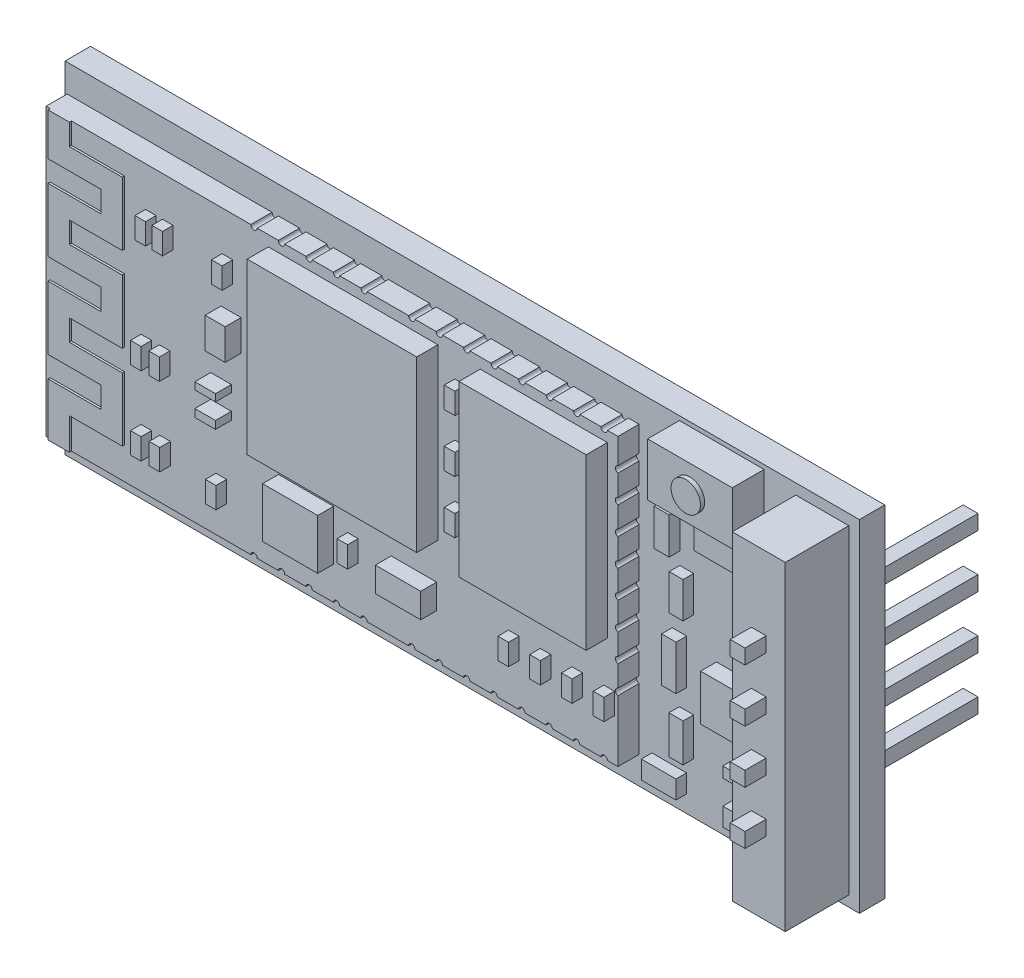
SolidWorks part; units mm, degrees
material "E-Glass Fiber"
ref_plane "Top Plane" through (0, 0, 0) normal (0, 0, 1) x (1, 0, 0)
ref_plane "Front Plane" through (0, 0, 0) normal (0, 1, 0) x (1, 0, 0)
ref_plane "Right Plane" through (0, 0, 0) normal (1, 0, 0) x (0, 0, -1)
sketch "Sketch1" plane through (0, 0, 0) normal (0, 0, 1) x (1, 0, 0)
  line L1 (0, 0) -> (37.5, 0)
  line L2 (0, 0) -> (0, 16.1)
  line L3 (0, 16.1) -> (37.5, 16.1)
  line L4 (37.5, 0) -> (37.5, 16.1)
  dimension "D1" = 37.5
  dimension "D2" = 16.1
extrude "Boss-Extrude1" add sketch "Sketch1" along normal blind 1.2
sketch "Sketch2" plane through (0, 0, 1.2) normal (0, 0, 1) x (1, 0, 0)
  line L0 (37.5, 0) -> (37.5, 16.1) construction
  line L1 (34.5, 0.5) -> (37, 0.5)
  line L2 (34.5, 0.5) -> (34.5, 15.6)
  line L3 (34.5, 15.6) -> (37, 15.6)
  line L4 (37, 0.5) -> (37, 15.6)
  line L5 (0, 0) -> (37.5, 0) construction
  line L6 (37.5, 16.1) -> (0, 16.1) construction
  dimension "D1" = 0.5
  dimension "D2" = 0.5
  dimension "D3" = 0.5
  dimension "D4" = 2.5
extrude "Boss-Extrude2" add sketch "Sketch2" along normal blind 3
sketch "Sketch3" plane through (0, 0, 4.2) normal (0, 0, 1) x (1, 0, 0)
  line L0 (34.5, 3.05) -> (37, 3.05)
  line L1 (34.5, 15.6) -> (34.5, 0.5) construction
  line L3 (34.5, 5.55) -> (37, 5.55)
  line L4 (37, 0.5) -> (37, 15.6) construction
  line L5 (34.5, 8.05) -> (37, 8.05)
  line L6 (34.5, 10.55) -> (37, 10.55)
  line L7 (34.5, 15.6) -> (34.5, 0.5) construction
  line L8 (34.5, 13.05) -> (37, 13.05)
  line L9 (37, 0.5) -> (37, 15.6) construction
  line L10 (34.5, 0.55) -> (37, 0.55)
  line L11 (34.5, 15.55) -> (37, 15.55)
  line L12 (37, 15.6) -> (34.5, 15.6) construction
  line L13 (34.5, 0.5) -> (37, 0.5) construction
  line L14 (35.4, 4.65) -> (36.1, 4.65)
  line L15 (35.4, 2.15) -> (36.1, 2.15) construction
  line L16 (35.4, 2.15) -> (35.4, 1.45) construction
  line L17 (35.4, 1.45) -> (36.1, 1.45) construction
  line L18 (36.1, 2.15) -> (36.1, 1.45) construction
  line L19 (35.4, 4.65) -> (35.4, 3.95)
  line L20 (35.4, 3.95) -> (36.1, 3.95)
  line L21 (36.1, 4.65) -> (36.1, 3.95)
  line L22 (35.4, 7.15) -> (36.1, 7.15)
  line L23 (35.4, 7.15) -> (35.4, 6.45)
  line L24 (35.4, 6.45) -> (36.1, 6.45)
  line L25 (36.1, 7.15) -> (36.1, 6.45)
  line L26 (35.4, 12.15) -> (36.1, 12.15)
  line L27 (35.4, 12.15) -> (35.4, 11.45)
  line L28 (35.4, 11.45) -> (36.1, 11.45)
  line L29 (36.1, 12.15) -> (36.1, 11.45)
  line L30 (35.4, 9.65) -> (36.1, 9.65)
  line L31 (35.4, 9.65) -> (35.4, 8.95)
  line L32 (35.4, 8.95) -> (36.1, 8.95)
  line L33 (36.1, 9.65) -> (36.1, 8.95)
  line L34 (35.4, 14.65) -> (36.1, 14.65) construction
  line L35 (35.4, 14.65) -> (35.4, 13.95) construction
  line L36 (35.4, 13.95) -> (36.1, 13.95) construction
  line L37 (36.1, 14.65) -> (36.1, 13.95) construction
  dimension "D1" = 0.05
  dimension "D2" = 0.05
  dimension "D3" = 2.5
  dimension "D4" = 2.5
  dimension "D5" = 2.5
  dimension "D6" = 2.5
  dimension "D7" = 2.5
  dimension "D8" = 0.7
  dimension "D9" = 0.7
  dimension "D10" = 0.9
  dimension "D11" = 0.9
  dimension "D12" = 0.7
  dimension "D13" = 0.7
  dimension "D14" = 0.9
  dimension "D15" = 0.9
  dimension "D16" = 0.9
  dimension "D17" = 0.9
  dimension "D18" = 0.7
  dimension "D19" = 0.7
  dimension "D20" = 0.9
  dimension "D21" = 0.9
  dimension "D22" = 0.7
  dimension "D23" = 0.7
  dimension "D24" = 0.9
  dimension "D25" = 0.9
  dimension "D26" = 0.7
  dimension "D27" = 0.7
  dimension "D28" = 0.9
  dimension "D29" = 0.7
  dimension "D30" = 0.9
  dimension "D31" = 0.7
extrude "Boss-Extrude3" add sketch "Sketch3" along normal blind 1 and the other way blind 10 separate body contours L18 L15 L16 L17 | L21 L14 L19 L20 | L33 L30 L31 L32 | L29 L26 L27 L28 | L37 L34 L35 L36 | L25 L24 L23 L22
sketch "Sketch10" plane through (0, 0, 1.2) normal (0, 0, 1) x (1, 0, 0)
  line L1 (0.1, 14.8) -> (27.1, 14.8)
  line L2 (0.1, 14.8) -> (0.1, 1.3)
  line L3 (0.1, 1.3) -> (27.1, 1.3)
  line L4 (27.1, 14.8) -> (27.1, 1.3)
  line L5 (37.5, 16.1) -> (0, 16.1) construction
  line L7 (0, 16.1) -> (0, 0) construction
  point P6 (0, 8.05)
  dimension "D1" = 13.5
  dimension "D2" = 27
  dimension "D3" = 1.3
  dimension "D4" = 0.1
extrude "Boss-Extrude10" add sketch "Sketch10" along normal blind 1
sketch "Sketch11" plane through (0, 0, 2.2) normal (0, 0, 1) x (1, 0, 0)
  line L0 (0.3, 1.3) -> (0.3, 14.8) construction
  line L1 (0.1, 1.3) -> (27.1, 1.3) construction
  line L2 (27.1, 14.8) -> (0.1, 14.8) construction
  line L3 (0.1, 14.8) -> (0.1, 1.3) construction
  line L4 (3.8, 14.8) -> (3.8, 1.3) construction
  line L5 (0.3, 1.3) -> (0.3, 3.8)
  line L6 (1.3, 2.8) -> (3.8, 2.8)
  line L7 (3.8, 2.8) -> (3.8, 5.8)
  line L8 (0.3, 3.8) -> (2.8, 3.8)
  line L9 (1.3, 1.3) -> (1.3, 2.8)
  line L10 (0.1, 1.3) -> (27.1, 1.3) construction
  line L11 (2.8, 3.8) -> (2.8, 4.8)
  line L12 (2.8, 4.8) -> (0.3, 4.8)
  line L13 (0.3, 4.8) -> (0.3, 7.8)
  line L14 (0.3, 7.8) -> (2.8, 7.8)
  line L15 (3.8, 5.8) -> (1.3, 5.8)
  line L16 (1.3, 5.8) -> (1.3, 6.8)
  line L17 (1.3, 6.8) -> (3.8, 6.8)
  line L18 (3.8, 6.8) -> (3.8, 9.8)
  line L19 (2.8, 7.8) -> (2.8, 8.8)
  line L20 (2.8, 8.8) -> (0.3, 8.8)
  line L21 (0.3, 8.8) -> (0.3, 11.8)
  line L22 (3.8, 9.8) -> (1.3, 9.8)
  line L23 (1.3, 9.8) -> (1.3, 10.8)
  line L24 (1.3, 10.8) -> (3.8, 10.8)
  line L25 (3.8, 10.8) -> (3.8, 13.8)
  line L26 (0.3, 11.8) -> (2.8, 11.8)
  line L27 (2.8, 11.8) -> (2.8, 12.8)
  line L28 (2.8, 12.8) -> (0.3, 12.8)
  line L29 (0.3, 12.8) -> (0.3, 14.8)
  line L30 (3.8, 13.8) -> (1.3, 13.8)
  line L31 (1.3, 13.8) -> (1.3, 14.8)
  line L32 (1.3, 14.8) -> (0.3, 14.8)
  line L33 (1.3, 1.3) -> (0.3, 1.3)
  dimension "D1" = 0.2
  dimension "D2" = 3.5
  dimension "D3" = 2.5
  dimension "D4" = 1
  dimension "D5" = 1.5
  dimension "D6" = 3
  dimension "D7" = 1
  dimension "D8" = 1
  dimension "D9" = 1
  dimension "D10" = 1
  dimension "D11" = 1
  dimension "D12" = 2.5
  dimension "D13" = 3
  dimension "D14" = 2.5
  dimension "D15" = 3
  dimension "D16" = 1
  dimension "D17" = 1
  dimension "D18" = 1
  dimension "D19" = 2.5
  dimension "D20" = 2.5
  dimension "D21" = 1
  dimension "D22" = 3
  dimension "D23" = 1
extrude "Boss-Extrude11" add sketch "Sketch11" along normal blind 0.1
sketch "Sketch12" plane through (0, 0, 1.2) normal (0, 0, 1) x (1, 0, 0)
  line L0 (37.5, 16.1) -> (0, 16.1) construction
  line L1 (29, 15.9) -> (33, 15.9)
  line L2 (29, 15.9) -> (29, 13.4)
  line L3 (29, 13.4) -> (33, 13.4)
  line L4 (33, 15.9) -> (33, 13.4)
  line L5 (34.5, 15.6) -> (34.5, 0.5) construction
  dimension "D1" = 2.5
  dimension "D2" = 4
  dimension "D3" = 0.2
  dimension "D4" = 1.5
extrude "Boss-Extrude12" add sketch "Sketch12" along normal blind 1.5 separate body
sketch "Sketch13" plane through (0, 0, 2.7) normal (0, 0, 1) x (1, 0, 0)
  line L0 (29, 14.65) -> (33, 14.65) construction
  line L1 (29, 15.9) -> (29, 13.4) construction
  line L2 (33, 13.4) -> (33, 15.9) construction
  line L3 (31, 15.9) -> (31, 13.4) construction
  line L4 (33, 15.9) -> (29, 15.9) construction
  line L5 (29, 13.4) -> (33, 13.4) construction
  circle A0 centre (31, 14.65) radius 0.6936
extrude "Boss-Extrude13" add sketch "Sketch13" along normal blind 0.2
sketch "Sketch14" plane through (0, 0, 2.2) normal (0, 0, 1) x (1, 0, 0)
  line L0 (27.1, 14.8) -> (1.3, 14.8) construction
  line L1 (26.6004, 6.3) -> (20.6004, 6.3)
  line L2 (26.6004, 6.3) -> (26.6004, 14.3)
  line L3 (26.6004, 14.3) -> (20.6004, 14.3)
  line L4 (20.6004, 6.3) -> (20.6004, 14.3)
  line L5 (27.1, 1.3) -> (27.1, 14.8) construction
  line L7 (18.6004, 6.3) -> (10.6004, 6.3)
  line L8 (18.6004, 6.3) -> (18.6004, 14.3)
  line L9 (18.6004, 14.3) -> (10.6004, 14.3)
  line L10 (10.6004, 6.3) -> (10.6004, 14.3)
  dimension "D1" = 8
  dimension "D2" = 6
  dimension "D3" = 0.5
  dimension "D4" = 0.4996
  dimension "D5" = 2
  dimension "D6" = 8
  dimension "D7" = 8
  dimension "D8" = 0.5
extrude "Boss-Extrude14" add sketch "Sketch14" along normal blind 1
sketch "Sketch15" plane through (0, 0, 2.2) normal (0, 0, 1) x (1, 0, 0)
  line L0 (3.8, 10.8) -> (3.8, 13.8) construction
  line L1 (4.8, 11.93) -> (5.3, 11.93)
  line L2 (4.8, 11.93) -> (4.8, 12.93)
  line L3 (4.8, 12.93) -> (5.3, 12.93)
  line L4 (5.3, 11.93) -> (5.3, 12.93)
  line L5 (5.6, 11.93) -> (6.1, 11.93)
  line L6 (5.6, 11.93) -> (5.6, 12.93)
  line L7 (5.6, 12.93) -> (6.1, 12.93)
  line L8 (6.1, 11.93) -> (6.1, 12.93)
  line L9 (8.4157, 11.93) -> (8.9157, 11.93)
  line L10 (8.4157, 11.93) -> (8.4157, 12.93)
  line L11 (8.4157, 12.93) -> (8.9157, 12.93)
  line L12 (8.9157, 11.93) -> (8.9157, 12.93)
  dimension "D1" = 1
  dimension "D2" = 0.5
  dimension "D3" = 1
  dimension "D4" = 0.5
  dimension "D5" = 1
  dimension "D6" = 0.5
  dimension "D7" = 1
  dimension "D8" = 0.3
extrude "Boss-Extrude15" add sketch "Sketch15" along normal blind 0.5
sketch "Sketch16" plane through (0, 0, 2.2) normal (0, 0, 1) x (1, 0, 0)
  line L0 (4.589, 6.722) -> (5.089, 6.722)
  line L1 (4.589, 6.722) -> (4.589, 7.722)
  line L2 (4.589, 7.722) -> (5.089, 7.722)
  line L3 (5.089, 6.722) -> (5.089, 7.722)
  line L4 (5.4516, 6.722) -> (5.9516, 6.722)
  line L5 (5.4516, 6.722) -> (5.4516, 7.722)
  line L6 (5.4516, 7.722) -> (5.9516, 7.722)
  line L7 (5.9516, 6.722) -> (5.9516, 7.722)
  line L8 (4.5888, 3.0335) -> (5.0888, 3.0335)
  line L9 (4.5888, 3.0335) -> (4.5888, 4.0335)
  line L10 (4.5888, 4.0335) -> (5.0888, 4.0335)
  line L11 (5.0888, 3.0335) -> (5.0888, 4.0335)
  line L12 (5.4701, 3.0335) -> (5.9701, 3.0335)
  line L13 (5.4701, 3.0335) -> (5.4701, 4.0335)
  line L14 (5.4701, 4.0335) -> (5.9701, 4.0335)
  line L15 (5.9701, 3.0335) -> (5.9701, 4.0335)
  line L16 (8.1243, 2.8062) -> (8.6243, 2.8062)
  line L17 (8.1243, 2.8062) -> (8.1243, 3.8062)
  line L18 (8.1243, 3.8062) -> (8.6243, 3.8062)
  line L19 (8.6243, 2.8062) -> (8.6243, 3.8062)
  line L20 (19.4004, 12.3) -> (19.9004, 12.3)
  line L21 (19.4004, 12.3) -> (19.4004, 13.3)
  line L22 (19.4004, 13.3) -> (19.9004, 13.3)
  line L23 (19.9004, 12.3) -> (19.9004, 13.3)
  line L24 (19.4004, 9.8) -> (19.9004, 9.8)
  line L25 (19.4004, 9.8) -> (19.4004, 10.8)
  line L26 (19.4004, 10.8) -> (19.9004, 10.8)
  line L27 (19.9004, 9.8) -> (19.9004, 10.8)
  line L28 (19.9004, 7.3) -> (19.4004, 7.3)
  line L29 (19.9004, 7.3) -> (19.9004, 8.3)
  line L30 (19.9004, 8.3) -> (19.4004, 8.3)
  line L31 (19.4004, 7.3) -> (19.4004, 8.3)
  line L32 (26.4351, 3.3) -> (26.9351, 3.3)
  line L33 (26.4351, 3.3) -> (26.4351, 4.3)
  line L34 (26.4351, 4.3) -> (26.9351, 4.3)
  line L35 (26.9351, 3.3) -> (26.9351, 4.3)
  line L36 (24.9351, 3.3) -> (25.4351, 3.3)
  line L37 (24.9351, 3.3) -> (24.9351, 4.3)
  line L38 (24.9351, 4.3) -> (25.4351, 4.3)
  line L39 (25.4351, 3.3) -> (25.4351, 4.3)
  line L40 (23.4351, 3.3) -> (23.9351, 3.3)
  line L41 (23.4351, 3.3) -> (23.4351, 4.3)
  line L42 (23.4351, 4.3) -> (23.9351, 4.3)
  line L43 (23.9351, 3.3) -> (23.9351, 4.3)
  line L44 (21.9351, 3.3) -> (22.4351, 3.3)
  line L45 (21.9351, 3.3) -> (21.9351, 4.3)
  line L46 (21.9351, 4.3) -> (22.4351, 4.3)
  line L47 (22.4351, 3.3) -> (22.4351, 4.3)
  line L48 (14.3404, 3.4908) -> (14.8404, 3.4908)
  line L49 (14.3404, 3.4908) -> (14.3404, 4.4908)
  line L50 (14.3404, 4.4908) -> (14.8404, 4.4908)
  line L51 (14.8404, 3.4908) -> (14.8404, 4.4908)
  line L52 (27.1, 14.8) -> (1.3, 14.8) construction
  line L54 (20.6004, 14.3) -> (20.6004, 6.3) construction
  line L55 (20.6004, 6.3) -> (26.6004, 6.3) construction
  dimension "D1" = 1
  dimension "D2" = 1
  dimension "D3" = 1
  dimension "D4" = 1
  dimension "D5" = 1
  dimension "D6" = 1
  dimension "D7" = 1
  dimension "D8" = 1
  dimension "D9" = 1
  dimension "D10" = 1
  dimension "D11" = 1
  dimension "D12" = 1
  dimension "D13" = 1
  dimension "D14" = 0.5
  dimension "D15" = 0.5
  dimension "D16" = 0.5
  dimension "D17" = 1.5
  dimension "D18" = 1.5
  dimension "D19" = 1.5
  dimension "D20" = 0.7
  dimension "D21" = 2
  dimension "D22" = 1
  dimension "D23" = 1
  dimension "D24" = 1
  dimension "D25" = 0.5
  dimension "D26" = 0.5
  dimension "D27" = 0.5
  dimension "D28" = 0.5
extrude "Boss-Extrude16" add sketch "Sketch16" along normal blind 0.5
sketch "Sketch17" plane through (0, 0, 2.2) normal (0, 0, 1) x (1, 0, 0)
  line L1 (11.0751, 2.8642) -> (13.6775, 2.8642)
  line L2 (11.0751, 2.8642) -> (11.0751, 5.2317)
  line L3 (11.0751, 5.2317) -> (13.6775, 5.2317)
  line L4 (13.6775, 2.8642) -> (13.6775, 5.2317)
  line L6 (16.3989, 3.3962) -> (18.5402, 3.3962)
  line L7 (16.3989, 3.3962) -> (16.3989, 4.5627)
  line L8 (16.3989, 4.5627) -> (18.5402, 4.5627)
  line L9 (18.5402, 3.3962) -> (18.5402, 4.5627)
  line L10 (7.8761, 6.3372) -> (8.8522, 6.3372)
  line L11 (7.8761, 6.3372) -> (7.8761, 6.7031)
  line L12 (7.8761, 6.7031) -> (8.8522, 6.7031)
  line L13 (8.8522, 6.3372) -> (8.8522, 6.7031)
  line L14 (7.8761, 7.4637) -> (8.8522, 7.4637)
  line L15 (7.8761, 7.4637) -> (7.8761, 7.7984)
  line L16 (7.8761, 7.7984) -> (8.8522, 7.7984)
  line L17 (8.8522, 7.4637) -> (8.8522, 7.7984)
  line L18 (8.3641, 9.3029) -> (9.3075, 9.3029)
  line L19 (8.3641, 9.3029) -> (8.3641, 10.7632)
  line L20 (8.3641, 10.7632) -> (9.3075, 10.7632)
  line L21 (9.3075, 9.3029) -> (9.3075, 10.7632)
extrude "Boss-Extrude17" add sketch "Sketch17" along normal blind 0.75
sketch "Sketch18" plane through (0, 0, 1.2) normal (0, 0, 1) x (1, 0, 0)
  line L1 (30.2001, 11.4276) -> (32.9069, 11.4276)
  line L2 (30.2001, 11.4276) -> (30.2001, 13.1705)
  line L3 (30.2001, 13.1705) -> (32.9069, 13.1705)
  line L4 (32.9069, 11.4276) -> (32.9069, 13.1705)
  line L5 (28.3044, 10.5724) -> (29.0208, 10.5724)
  line L6 (28.3044, 10.5724) -> (28.3044, 12.2991)
  line L7 (28.3044, 12.2991) -> (29.0208, 12.2991)
  line L8 (29.0208, 10.5724) -> (29.0208, 12.2991)
  line L9 (29.0208, 8.2903) -> (29.6736, 8.2903)
  line L10 (29.0208, 8.2903) -> (29.0208, 9.9841)
  line L11 (29.0208, 9.9841) -> (29.6736, 9.9841)
  line L12 (29.6736, 8.2903) -> (29.6736, 9.9841)
  line L13 (28.6626, 5.1548) -> (29.3472, 5.1548)
  line L14 (28.6626, 5.1548) -> (28.6626, 7.2612)
  line L15 (28.6626, 7.2612) -> (29.3472, 7.2612)
  line L16 (29.3472, 5.1548) -> (29.3472, 7.2612)
  line L17 (29.0049, 2.403) -> (29.6736, 2.403)
  line L18 (29.0049, 2.403) -> (29.0049, 4.2038)
  line L19 (29.0049, 4.2038) -> (29.6736, 4.2038)
  line L20 (29.6736, 2.403) -> (29.6736, 4.2038)
  line L21 (27.7053, 0.8007) -> (29.3393, 0.8007)
  line L22 (27.7053, 0.8007) -> (27.7053, 1.6631)
  line L23 (27.7053, 1.6631) -> (29.3393, 1.6631)
  line L24 (29.3393, 0.8007) -> (29.3393, 1.6631)
  line L25 (31.5535, 0.8007) -> (32.9069, 0.8007)
  line L26 (31.5535, 0.8007) -> (31.5535, 1.6631)
  line L27 (31.5535, 1.6631) -> (32.9069, 1.6631)
  line L28 (32.9069, 0.8007) -> (32.9069, 1.6631)
  line L29 (31.5535, 2.804) -> (32.9069, 2.804)
  line L30 (31.5535, 2.804) -> (31.5535, 3.3034)
  line L31 (31.5535, 3.3034) -> (32.9069, 3.3034)
  line L32 (32.9069, 2.804) -> (32.9069, 3.3034)
  line L33 (32.0202, 10.8077) -> (33.3885, 10.8077)
  line L34 (32.0202, 10.8077) -> (32.0202, 9.9841)
  line L35 (32.0202, 9.9841) -> (33.3885, 9.9841)
  line L36 (33.3885, 10.8077) -> (33.3885, 9.9841)
  line L37 (32.0202, 8.2903) -> (33.3885, 8.2903)
  line L38 (32.0202, 8.2903) -> (32.0202, 9.082)
  line L39 (32.0202, 9.082) -> (33.3885, 9.082)
  line L40 (33.3885, 8.2903) -> (33.3885, 9.082)
extrude "Boss-Extrude18" add sketch "Sketch18" along normal blind 0.5
sketch "Sketch19" plane through (0, 0, 1.2) normal (0, 0, 1) x (1, 0, 0)
  line L1 (30.7569, 4.7405) -> (33.8081, 4.7405)
  line L2 (30.7569, 4.7405) -> (30.7569, 6.9062)
  line L3 (30.7569, 6.9062) -> (33.8081, 6.9062)
  line L4 (33.8081, 4.7405) -> (33.8081, 6.9062)
extrude "Boss-Extrude19" add sketch "Sketch19" along normal blind 0.75
sketch "Sketch20" plane through (0, 0, 2.2) normal (0, 0, 1) x (1, 0, 0)
  line L0 (27.1, 14.8) -> (1.3, 14.8) construction
  line L1 (27.1, 1.3) -> (27.1, 14.8) construction
  line L2 (26.6, 14.8) -> (26.3, 14.8)
  line L3 (25.3, 14.8) -> (25.0045, 14.8)
  line L4 (24.5045, 14.4582) -> (24.5045, 15.2412) construction
  line L5 (23.7089, 14.8) -> (24.0045, 14.8)
  line L6 (22.4089, 14.8) -> (22.7089, 14.8)
  line L7 (21.9089, 14.5317) -> (21.9089, 15.1738) construction
  line L8 (21.4089, 14.8) -> (21.1089, 14.8)
  line L9 (20.1089, 14.8) -> (19.8134, 14.8)
  line L10 (18.5179, 14.8) -> (18.8134, 14.8)
  line L11 (17.2179, 14.8) -> (17.5179, 14.8)
  line L12 (16.2399, 14.5317) -> (16.2399, 15.1738) construction
  line L13 (10.5708, 14.5317) -> (10.5708, 15.1738) construction
  line L14 (15.2619, 14.8) -> (14.9619, 14.8)
  line L15 (13.9619, 14.8) -> (13.6663, 14.8)
  line L16 (12.3708, 14.8) -> (12.6663, 14.8)
  line L17 (11.0708, 14.8) -> (11.3708, 14.8)
  line L18 (10.0708, 14.8) -> (9.7708, 14.8)
  line L19 (27.1, 8.05) -> (0.1, 8.05) construction
  line L20 (0.1, 14.8) -> (0.1, 1.3) construction
  line L21 (10.5708, 1.5683) -> (10.5708, 0.9262) construction
  line L22 (16.2399, 1.5683) -> (16.2399, 0.9262) construction
  line L23 (21.9089, 1.5683) -> (21.9089, 0.9262) construction
  line L24 (24.5045, 1.6418) -> (24.5045, 0.8588) construction
  line L25 (10.0708, 1.3) -> (9.7708, 1.3)
  line L26 (11.0708, 1.3) -> (11.3708, 1.3)
  line L27 (12.3708, 1.3) -> (12.6663, 1.3)
  line L28 (13.9619, 1.3) -> (13.6663, 1.3)
  line L29 (15.2619, 1.3) -> (14.9619, 1.3)
  line L30 (17.2179, 1.3) -> (17.5179, 1.3)
  line L31 (18.5179, 1.3) -> (18.8134, 1.3)
  line L32 (20.1089, 1.3) -> (19.8134, 1.3)
  line L33 (21.4089, 1.3) -> (21.1089, 1.3)
  line L34 (22.4089, 1.3) -> (22.7089, 1.3)
  line L35 (23.7089, 1.3) -> (24.0045, 1.3)
  line L36 (25.3, 1.3) -> (25.0045, 1.3)
  line L37 (26.6, 1.3) -> (26.3, 1.3)
  arc A0 (26.6, 14.8) -> (26.3, 14.8) centre (26.45, 14.8) cw
  arc A1 (25.3, 14.8) -> (25.0045, 14.8) centre (25.1522, 14.8) cw
  arc A2 (23.7089, 14.8) -> (24.0045, 14.8) centre (23.8567, 14.8) ccw
  arc A3 (22.4089, 14.8) -> (22.7089, 14.8) centre (22.5589, 14.8) ccw
  arc A4 (21.4089, 14.8) -> (21.1089, 14.8) centre (21.2589, 14.8) cw
  arc A5 (20.1089, 14.8) -> (19.8134, 14.8) centre (19.9612, 14.8) cw
  arc A6 (18.5179, 14.8) -> (18.8134, 14.8) centre (18.6656, 14.8) ccw
  arc A7 (17.2179, 14.8) -> (17.5179, 14.8) centre (17.3679, 14.8) ccw
  arc A8 (15.2619, 14.8) -> (14.9619, 14.8) centre (15.1119, 14.8) cw
  arc A9 (13.9619, 14.8) -> (13.6663, 14.8) centre (13.8141, 14.8) cw
  arc A10 (12.3708, 14.8) -> (12.6663, 14.8) centre (12.5186, 14.8) ccw
  arc A11 (11.0708, 14.8) -> (11.3708, 14.8) centre (11.2208, 14.8) ccw
  arc A12 (10.0708, 14.8) -> (9.7708, 14.8) centre (9.9208, 14.8) cw
  arc A13 (10.0708, 1.3) -> (9.7708, 1.3) centre (9.9208, 1.3) ccw
  arc A14 (11.0708, 1.3) -> (11.3708, 1.3) centre (11.2208, 1.3) cw
  arc A15 (12.3708, 1.3) -> (12.6663, 1.3) centre (12.5186, 1.3) cw
  arc A16 (13.9619, 1.3) -> (13.6663, 1.3) centre (13.8141, 1.3) ccw
  arc A17 (15.2619, 1.3) -> (14.9619, 1.3) centre (15.1119, 1.3) ccw
  arc A18 (17.2179, 1.3) -> (17.5179, 1.3) centre (17.3679, 1.3) cw
  arc A19 (18.5179, 1.3) -> (18.8134, 1.3) centre (18.6656, 1.3) cw
  arc A20 (20.1089, 1.3) -> (19.8134, 1.3) centre (19.9612, 1.3) ccw
  arc A21 (21.4089, 1.3) -> (21.1089, 1.3) centre (21.2589, 1.3) ccw
  arc A22 (22.4089, 1.3) -> (22.7089, 1.3) centre (22.5589, 1.3) cw
  arc A23 (23.7089, 1.3) -> (24.0045, 1.3) centre (23.8567, 1.3) cw
  arc A24 (25.3, 1.3) -> (25.0045, 1.3) centre (25.1522, 1.3) ccw
  arc A25 (26.6, 1.3) -> (26.3, 1.3) centre (26.45, 1.3) ccw
  dimension "D1" = 0.5
  dimension "D2" = 0.3
  dimension "D3" = 1
  dimension "D4" = 0.5
  dimension "D5" = 0.5
extrude "Cut-Extrude1" cut sketch "Sketch20" against normal blind 1
sketch "Sketch21" plane through (0, 0, 2.2) normal (0, 0, 1) x (1, 0, 0)
  line L0 (27.1, 1.3) -> (27.1, 14.8) construction
  line L1 (27.1, 13.3005) -> (27.1, 13.5998)
  line L2 (26.7694, 12.8005) -> (27.3012, 12.8005) construction
  line L3 (27.1, 12.3005) -> (27.1, 12.0011)
  line L4 (26.8075, 11.5011) -> (27.3621, 11.5011) construction
  line L5 (27.1, 10.7018) -> (27.1, 11.0011)
  line L6 (27.1, 9.7018) -> (27.1, 9.4024)
  line L7 (26.7694, 8.9024) -> (27.3621, 8.9024) construction
  line L8 (27.3621, 8.9024) -> (27.0657, 8.9024) construction
  line L9 (26.8075, 6.3037) -> (27.3621, 6.3037) construction
  line L10 (26.7694, 5.0044) -> (27.3012, 5.0044) construction
  line L11 (27.1, 8.1031) -> (27.1, 8.4024)
  line L12 (27.1, 7.1031) -> (27.1, 6.8037)
  line L13 (27.1, 5.5044) -> (27.1, 5.8037)
  line L14 (27.1, 4.5044) -> (27.1, 4.205)
  arc A0 (27.1, 13.5998) -> (27.1, 13.3005) centre (27.1317, 13.4502) ccw
  arc A1 (27.1, 12.0011) -> (27.1, 12.3005) centre (27.1317, 12.1508) cw
  arc A2 (27.1, 11.0011) -> (27.1, 10.7018) centre (27.1317, 10.8514) ccw
  arc A3 (27.1, 9.4024) -> (27.1, 9.7018) centre (27.1317, 9.5521) cw
  arc A4 (27.1, 8.4024) -> (27.1, 8.1031) centre (27.1317, 8.2527) ccw
  arc A5 (27.1, 6.8037) -> (27.1, 7.1031) centre (27.1317, 6.9534) cw
  arc A6 (27.1, 5.8037) -> (27.1, 5.5044) centre (27.1317, 5.654) ccw
  arc A7 (27.1, 4.205) -> (27.1, 4.5044) centre (27.1317, 4.3547) cw
  dimension "D1" = 0.5
  dimension "D2" = 0.5
  dimension "D3" = 0.5
extrude "Cut-Extrude2" cut sketch "Sketch21" against normal blind 1
